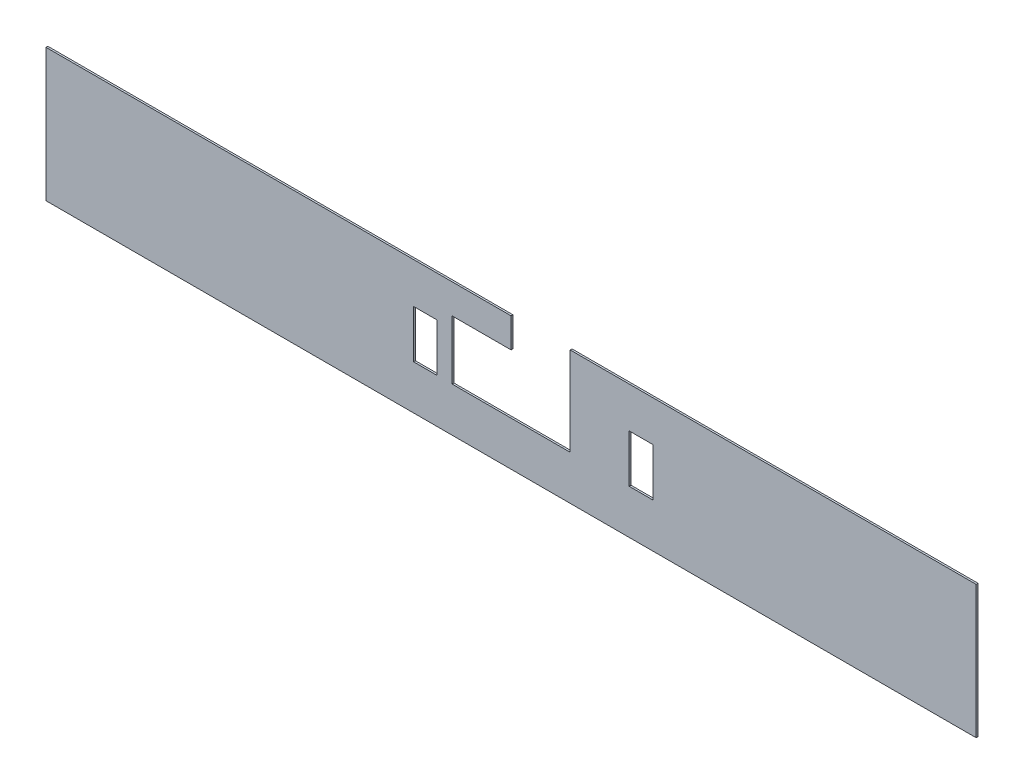
SolidWorks part; units mm, degrees
ref_plane "Front Plane" through (0, 0, 0) normal (0, 0, 1) x (1, 0, 0)
ref_plane "Top Plane" through (0, 0, 0) normal (0, 1, 0) x (1, 0, 0)
ref_plane "Right Plane" through (0, 0, 0) normal (1, 0, 0) x (0, 0, -1)
sketch "Sketch1" plane through (0, 0, 0) normal (0, 0, 1) x (1, 0, 0)
  line L0 (0, 0) -> (50.8, 0)
  line L1 (50.8, 0) -> (50.8, 76.2)
  line L2 (50.8, 76.2) -> (400.05, 76.2)
  line L3 (400.05, 76.2) -> (400.05, -38.1)
  line L4 (400.05, -38.1) -> (-400.05, -38.1)
  line L5 (-400.05, -38.1) -> (-400.05, 76.2)
  line L6 (-400.05, 76.2) -> (0, 76.2)
  line L7 (0, 76.2) -> (0, 0)
  line L8 (50.8, 0) -> (75.8269, 0.2451)
  dimension "D1" = 800.1
  dimension "D2" = 76.2
  dimension "D3" = 114.3
  dimension "D4" = 50.8
  dimension "D5" = 400.05
extrude "Boss-Extrude1" add sketch "Sketch1" along normal blind 1.6002 contours L1 L2 L3 L4 L5 L6 L7 L0
sketch "Sketch2" plane through (0, 0, 0) normal (0, 0, 1) x (1, 0, 0)
  line L0 (0, 76.2) -> (-400.05, 76.2) construction
  line L1 (-83.82, 41.275) -> (-63.5, 41.275)
  line L2 (-83.82, 41.275) -> (-83.82, 0)
  line L3 (-83.82, 0) -> (-63.5, 0)
  line L4 (-63.5, 41.275) -> (-63.5, 0)
  line L5 (-83.82, 41.275) -> (-63.5, 0) construction
  line L6 (-83.82, 0) -> (-63.5, 41.275) construction
  line L7 (0, 76.2) -> (0, 0) construction
  line L8 (50.8, 0) -> (50.8, 76.2) construction
  line L9 (101.6, 41.275) -> (121.92, 41.275)
  line L10 (101.6, 41.275) -> (101.6, 0)
  line L11 (101.6, 0) -> (121.92, 0)
  line L12 (121.92, 41.275) -> (121.92, 0)
  line L13 (101.6, 41.275) -> (121.92, 0) construction
  line L14 (101.6, 0) -> (121.92, 41.275) construction
  line L15 (50.8, 76.2) -> (400.05, 76.2) construction
  point P0 (-73.66, 20.6375)
  point P9 (111.76, 20.6375)
  dimension "D1" = 34.925
  dimension "D2" = 63.5
  dimension "D3" = 20.32
  dimension "D4" = 50.8
  dimension "D5" = 34.925
  dimension "D6" = 41.275
extrude "Cut-Extrude5" cut sketch "Sketch2" along normal through all
sketch "Sketch3" plane through (0, 0, 0) normal (0, 0, -1) x (-1, 0, 0)
  line L0 (400.05, 76.2) -> (0, 76.2) construction
  line L1 (0, 0) -> (50.8, 0)
  line L2 (0, 0) -> (0, 50.8)
  line L3 (0, 50.8) -> (50.8, 50.8)
  line L4 (50.8, 0) -> (50.8, 50.8)
  dimension "D1" = 25.4
  dimension "D2" = 50.8
extrude "Cut-Extrude6" cut sketch "Sketch3" against normal blind 2.54
